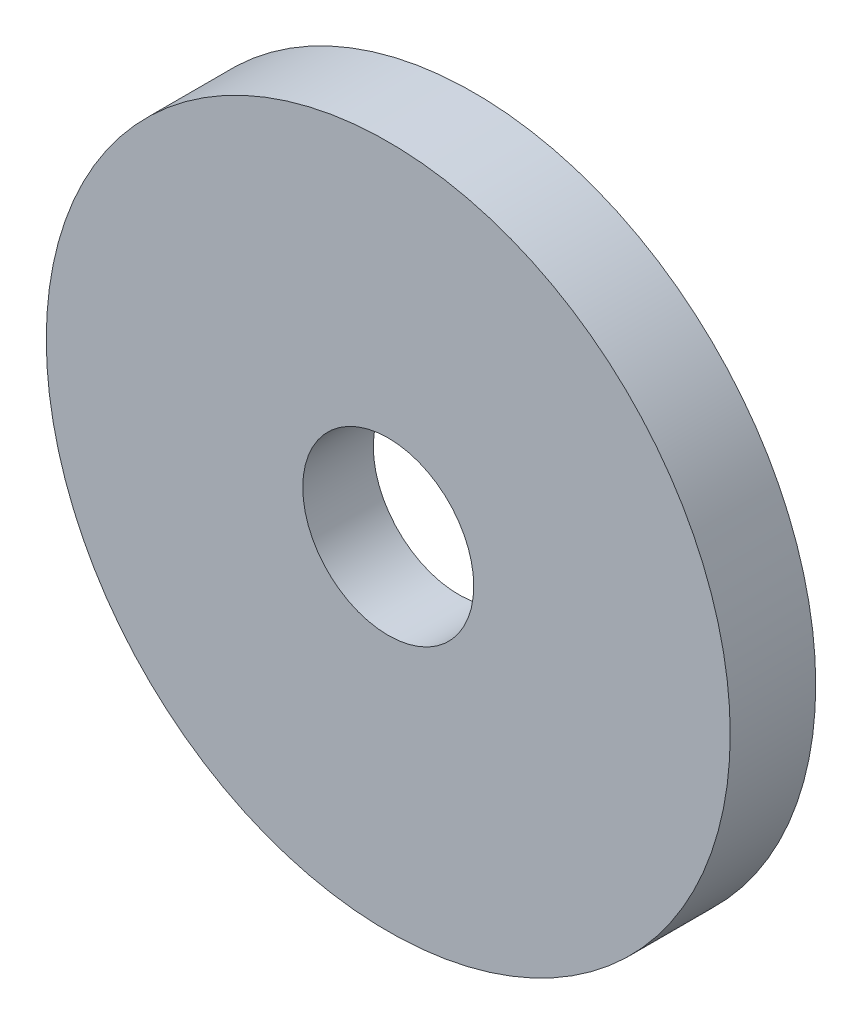
SolidWorks part; units mm, degrees
ref_plane "Front Plane" through (0, 0, 0) normal (0, 0, 1) x (1, 0, 0)
ref_plane "Top Plane" through (0, 0, 0) normal (0, 1, 0) x (1, 0, 0)
ref_plane "Right Plane" through (0, 0, 0) normal (1, 0, 0) x (0, 0, -1)
sketch "Croquis1" plane through (0, 0, 0) normal (0, 0, 1) x (1, 0, 0)
  circle A0 centre (0, 0) radius 1
  circle A1 centre (0, 0) radius 0.25
  dimension "D1" = 2
  dimension "D2" = 0.5
extrude "Saliente-Extruir1" add sketch "Croquis1" along normal blind 0.25
sketch "Croquis2" plane through (0, 0, 0) normal (0, 0, -1) x (-1, 0, 0)
  circle A0 centre (0, 0) radius 0.75
  dimension "D1" = 1.5
extrude "Cortar-Extruir1" cut sketch "Croquis2" against normal blind 0.1 draft 85
